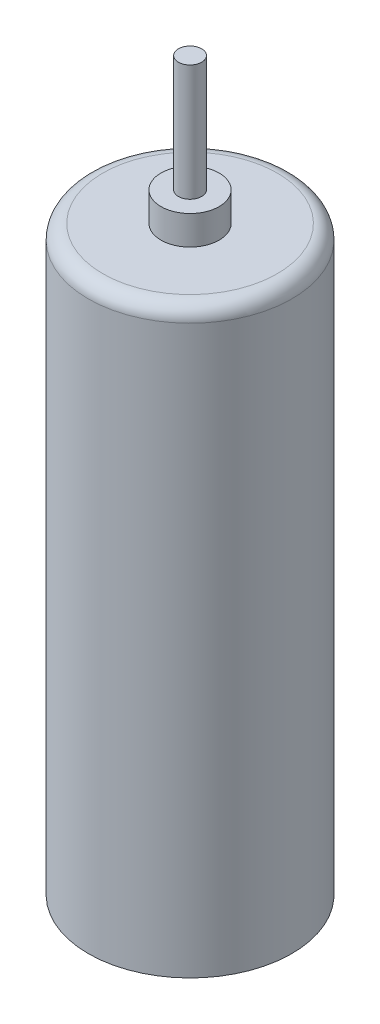
SolidWorks part; units mm, degrees
ref_plane "Front Plane" through (0, 0, 0) normal (0, 0, 1) x (1, 0, 0)
ref_plane "Top Plane" through (0, 0, 0) normal (0, 1, 0) x (1, 0, 0)
ref_plane "Right Plane" through (0, 0, 0) normal (1, 0, 0) x (0, 0, -1)
sketch "Sketch1" plane through (0, 0, 0) normal (0, 1, 0) x (1, 0, 0)
  circle A0 centre (0, 0) radius 3.5
  dimension "D1" = 7
extrude "Boss-Extrude1" add sketch "Sketch1" along normal blind 20
sketch "Sketch2" plane through (0, 20, 0) normal (0, 1, 0) x (1, 0, 0)
  circle A0 centre (0, 0) radius 1
  dimension "D1" = 2
extrude "Boss-Extrude2" add sketch "Sketch2" along normal blind 1
sketch "Sketch3" plane through (0, 20, 0) normal (0, 1, 0) x (1, 0, 0)
  circle A0 centre (0, 0) radius 0.4
  dimension "D1" = 0.8
extrude "Boss-Extrude3" add sketch "Sketch3" along normal blind 5
fillet "Fillet1" radius 0.5 1 edges at (0, 20, 3.5)
